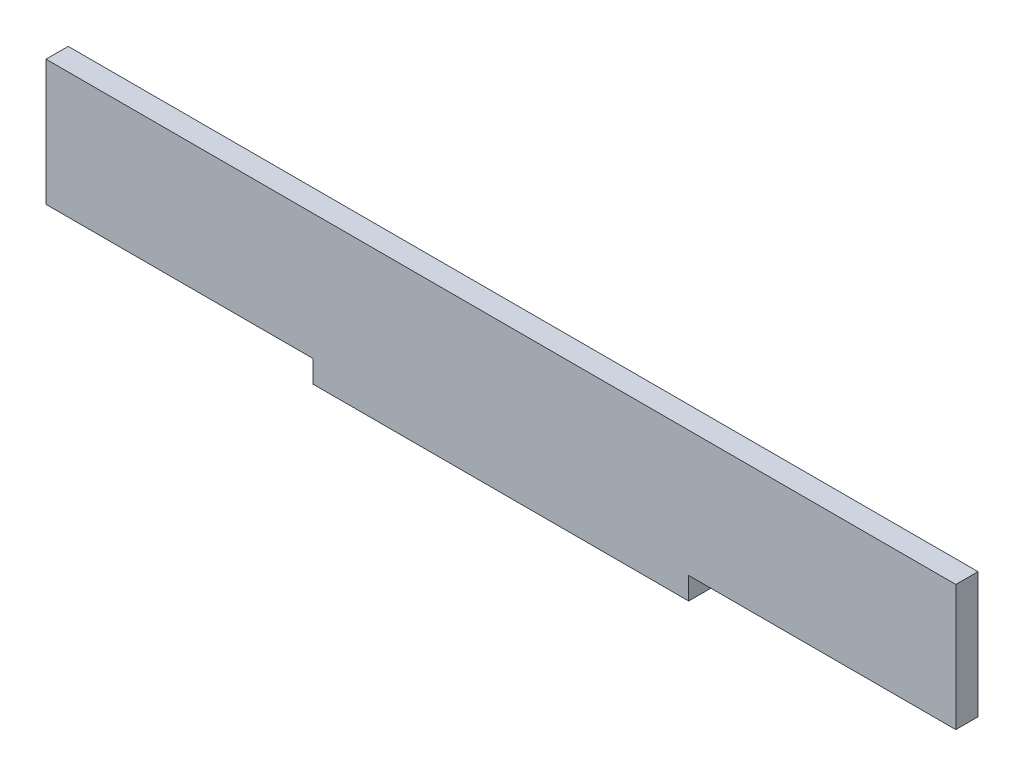
SolidWorks part; units mm, degrees
ref_plane "Front Plane" through (0, 0, 0) normal (0, 0, 1) x (1, 0, 0)
ref_plane "Top Plane" through (0, 0, 0) normal (0, 1, 0) x (1, 0, 0)
ref_plane "Right Plane" through (0, 0, 0) normal (1, 0, 0) x (0, 0, -1)
sketch "Sketch1" plane through (0, 0, 0) normal (0, 0, 1) x (1, 0, 0)
  line L0 (25.3868, -8.5) -> (61.5, -8.5)
  line L1 (-61.5, 8.5) -> (61.5, 8.5)
  line L2 (-61.5, 8.5) -> (-61.5, -8.5)
  line L3 (-61.5, -8.5) -> (-25.3868, -8.5)
  line L4 (61.5, 8.5) -> (61.5, -8.5)
  line L7 (-25.3868, -11.5) -> (25.3868, -11.5)
  line L8 (-25.3868, -11.5) -> (-25.3868, -8.5)
  line L10 (25.3868, -11.5) -> (25.3868, -8.5)
  point P0 (0, 0)
  point P6 (0, -10)
  point P11 (0, 0)
  point P12 (0, 0)
  dimension "D1" = 123
  dimension "D2" = 17
extrude "Boss-Extrude1" add sketch "Sketch1" along normal blind 3
